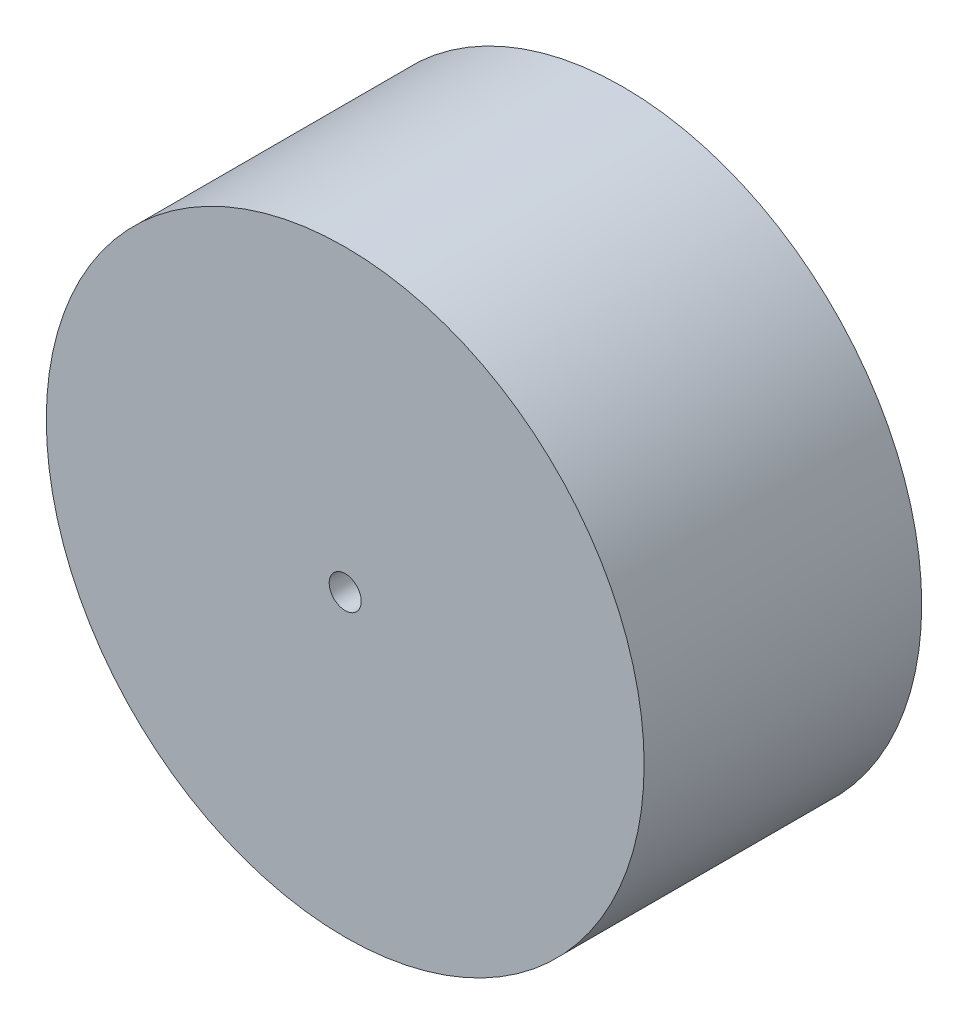
SolidWorks part; units mm, degrees
ref_plane "前基準面" through (0, 0, 0) normal (0, 0, 1) x (1, 0, 0)
ref_plane "上基準面" through (0, 0, 0) normal (0, 1, 0) x (1, 0, 0)
ref_plane "右基準面" through (0, 0, 0) normal (1, 0, 0) x (0, 0, -1)
sketch "草圖1" plane through (0, 0, 0) normal (0, 0, 1) x (1, 0, 0)
  circle A0 centre (0, 0) radius 28
  circle A1 centre (0, 0) radius 1.5
extrude "填料-伸長1" add sketch "草圖1" along normal blind 26
